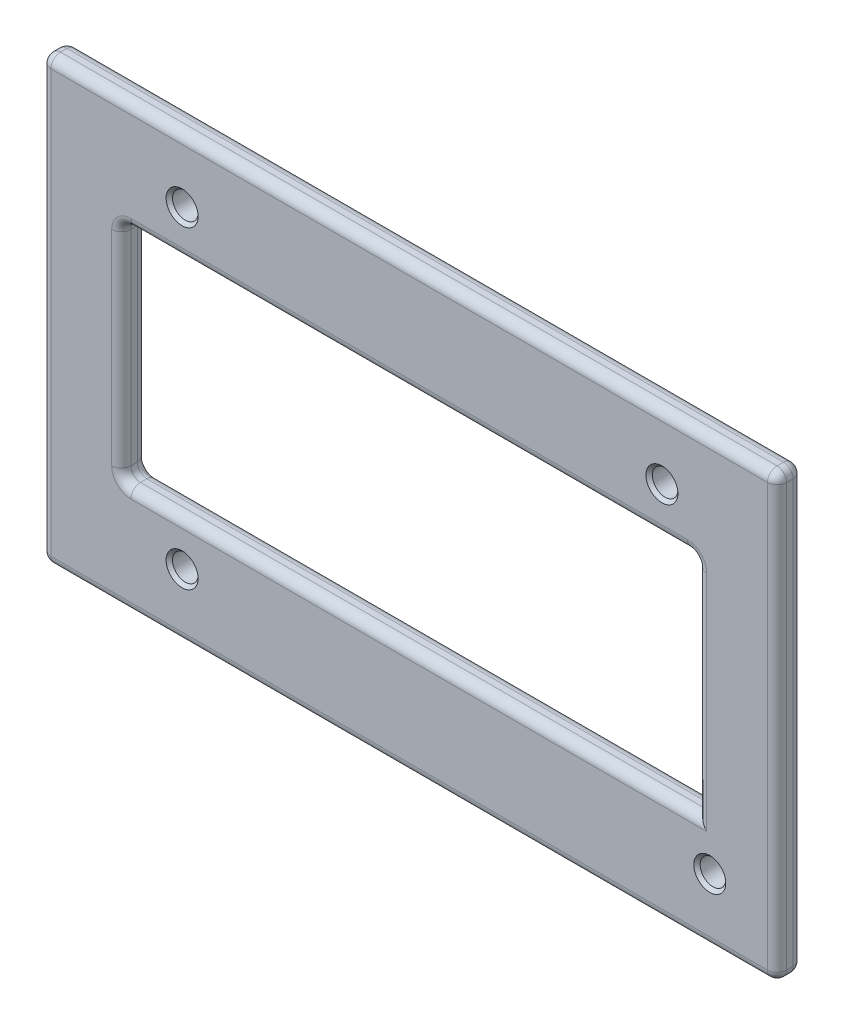
SolidWorks part; units mm, degrees
material "ABS"
ref_plane "Front Plane" through (0, 0, 0) normal (0, 0, 1) x (1, 0, 0)
ref_plane "Top Plane" through (0, 0, 0) normal (0, 1, 0) x (1, 0, 0)
ref_plane "Right Plane" through (0, 0, 0) normal (1, 0, 0) x (0, 0, -1)
sketch "Sketch1" plane through (0, 0, 0) normal (0, 0, 1) x (1, 0, 0)
  line L5 (-57.5, -34.5) -> (57.5, -34.5)
  line L6 (-57.5, -34.5) -> (-57.5, 34.5)
  line L11 (-57.5, 34.5) -> (57.5, 34.5)
  line L12 (57.5, -34.5) -> (57.5, 34.5)
  line L13 (-57.5, -34.5) -> (57.5, 34.5) construction
  line L14 (-57.5, 34.5) -> (57.5, -34.5) construction
  point P0 (0, 0)
  dimension "D1" = 115
  dimension "D2" = 69
extrude "Boss-Extrude1" add sketch "Sketch1" along normal blind 4
sketch "Sketch2" plane through (0, 0, 4) normal (0, 0, 1) x (1, 0, 0)
  line L0 (57.696, 0) -> (-57.5, 0) construction
  line L1 (-35.5, -24.5) -> (-35.5, 24.5) construction
  line L2 (-35.5, 24.5) -> (39.5, 24.5) construction
  line L3 (-42.5, -28) -> (42.5, -28) construction
  line L4 (-42.5, -28) -> (-42.5, 28) construction
  line L5 (-42.5, 28) -> (42.5, 28) construction
  line L6 (42.5, -28) -> (42.5, 28) construction
  line L7 (-42.5, -28) -> (42.5, 28) construction
  line L8 (-42.5, 28) -> (42.5, -28) construction
  line L10 (-57.5, 34.5) -> (-57.5, -34.5) construction
  circle A0 centre (-35.5, 24.5) radius 2
  circle A1 centre (39.5, 24.5) radius 2
  circle A2 centre (46.979, -24.5) radius 2
  circle A3 centre (-35.5, -24.5) radius 2
  point P0 (0, 0)
  point P11 (0, 0)
  dimension "D3" = 4
  dimension "D1" = 75
  dimension "D2" = 49
  dimension "D4" = 85
  dimension "D5" = 56
  dimension "D6" = 82.479
  dimension "D7" = 49
  dimension "D8" = 7
  dimension "D9" = 15
extrude "Cut-Extrude1" cut sketch "Sketch2" against normal blind 4
sketch "Sketch3" plane through (0, 0, 4) normal (0, 0, 1) x (1, 0, 0)
  line L1 (-45, -17.5) -> (45, -17.5)
  line L2 (-45, -17.5) -> (-45, 17.5)
  line L3 (-45, 17.5) -> (45, 17.5)
  line L4 (45, -17.5) -> (45, 17.5)
  line L5 (-45, -17.5) -> (45, 17.5) construction
  line L6 (-45, 17.5) -> (45, -17.5) construction
  point P0 (0, 0)
  dimension "D1" = 90
  dimension "D2" = 35
extrude "Cut-Extrude2" cut sketch "Sketch3" against normal blind 4
chamfer "Chamfer1" distance 0.5 angle 45 4 edges at (48.979, -24.5, 4) (41.5, 24.5, 4) (-33.5, -24.5, 4) (-33.5, 24.5, 4)
fillet "Fillet1" radius 1.5 23 edges at (-45, -17.5, 2) (-45, 17.5, 2) (-45, 0, 0) (-45, 0, 4) (0, -17.5, 0) (0, -17.5, 4) (45, 17.5, 2) (45, 0, 0) (45, 0, 4) (0, 17.5, 0) (0, 17.5, 4) (-57.5, -34.5, 2) (-57.5, 34.5, 2) (-57.5, 0, 0) (-57.5, 0, 4) (0, 34.5, 0) (0, 34.5, 4) (57.5, 34.5, 2) (57.5, -34.5, 2) (0, -34.5, 0) (0, -34.5, 4) (57.5, 0, 0) (57.5, 0, 4)
